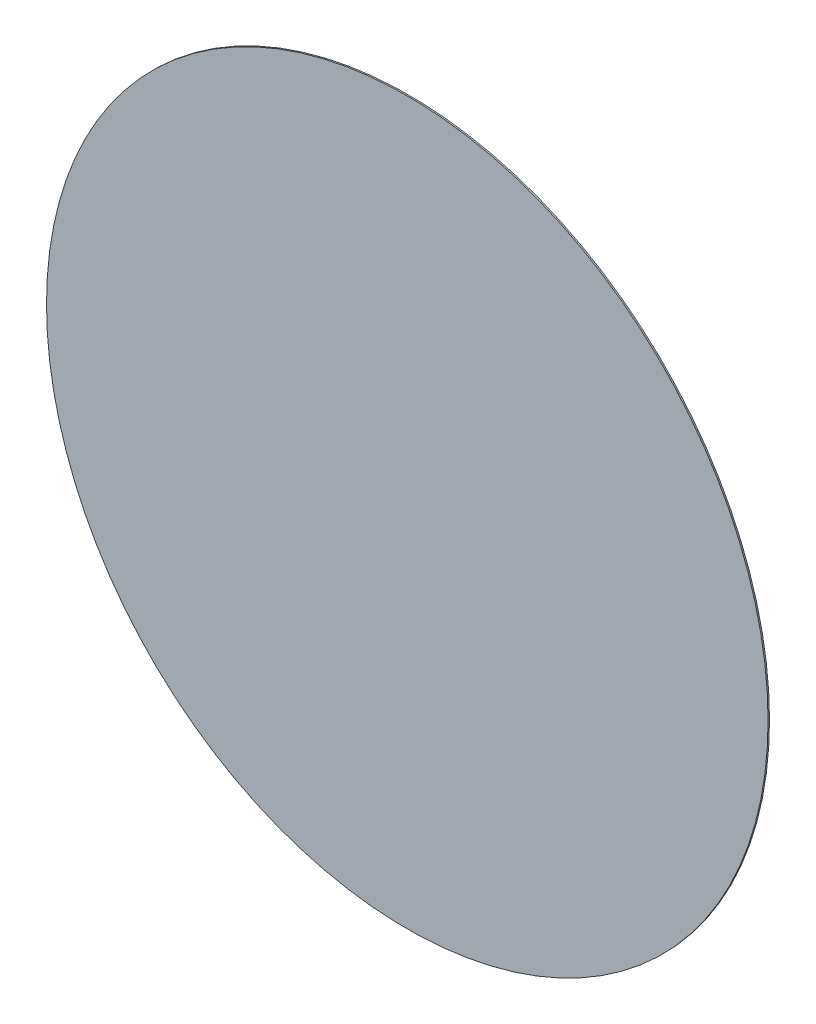
SolidWorks part; units mm, degrees
material "PEI"
ref_plane "Front Plane" through (0, 0, 0) normal (0, 0, 1) x (1, 0, 0)
ref_plane "Top Plane" through (0, 0, 0) normal (0, 1, 0) x (1, 0, 0)
ref_plane "Right Plane" through (0, 0, 0) normal (1, 0, 0) x (0, 0, -1)
sketch "Sketch1" plane through (0, 0, 0) normal (0, 0, 1) x (1, 0, 0)
  circle A0 centre (0, 0) radius 127
  dimension "D1" = 254
extrude "Boss-Extrude1" add sketch "Sketch1" along normal blind 0.5
